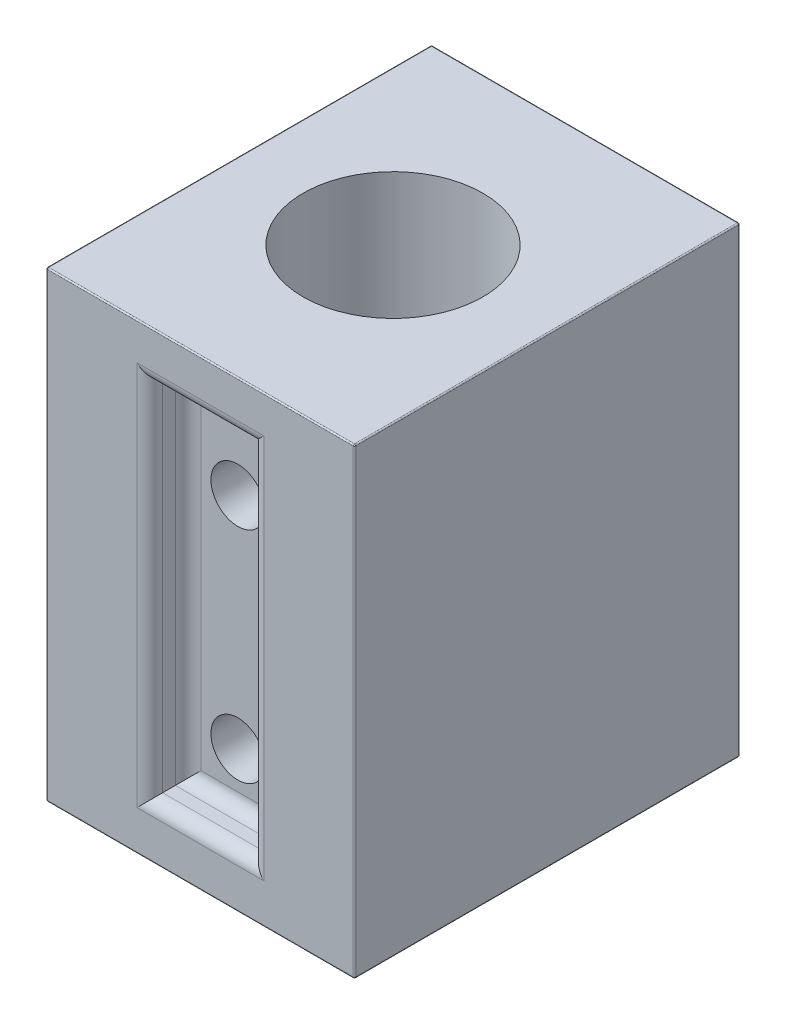
SolidWorks part; units mm, degrees
ref_plane "Front" through (0, 0, 0) normal (0, 0, 1) x (1, 0, 0)
ref_plane "Top" through (0, 0, 0) normal (0, 1, 0) x (1, 0, 0)
ref_plane "Right" through (0, 0, 0) normal (1, 0, 0) x (0, 0, -1)
sketch "Sketch2" plane through (0, 0, 0) normal (0, 0, 1) x (1, 0, 0)
  line L1 (-6, 9) -> (6, 9)
  line L2 (-6, 9) -> (-6, -9)
  line L3 (-6, -9) -> (6, -9)
  line L4 (6, 9) -> (6, -9)
  line L5 (-6, 9) -> (6, -9) construction
  line L6 (-6, -9) -> (6, 9) construction
  point P0 (0, 0)
  dimension "D1" = 12
  dimension "D2" = 18
extrude "Boss-Extrude1" add sketch "Sketch2" along normal blind 15
sketch "Sketch5" plane through (0, -9, 0) normal (0, -1, 0) x (-1, 0, 0)
  line L0 (6, -15) -> (-6, 0) construction
  line L1 (6, -15) -> (-6, -15) construction
  line L2 (-6, -15) -> (6, 0) construction
  line L3 (6, -15) -> (6, 0) construction
  circle A0 centre (0, -7.5) radius 3.5
  dimension "D1" = 7
extrude "Cut-Extrude2" cut sketch "Sketch5" against normal blind 18
sketch "Sketch8" plane through (0, 0, 15) normal (0, 0, 1) x (1, 0, 0)
  line L1 (-1.9685, 7.05) -> (1.9685, 7.05)
  line L2 (-1.9685, 7.05) -> (-1.9685, -6.95)
  line L3 (-1.9685, -6.95) -> (1.9685, -6.95)
  line L4 (1.9685, 7.05) -> (1.9685, -6.95)
  line L6 (6, 9) -> (-6, 9) construction
  point P6 (0, 9)
  point P7 (0, 7.05)
  dimension "D1" = 14
  dimension "D2" = 3.937
  dimension "D3" = 1.95
extrude "Cut-Extrude3" cut sketch "Sketch8" against normal blind 1.4928
fillet "Fillet3" radius 0.05 12 edges at (6, -9, 7.5) (6, 0, 15) (6, 9, 7.5) (6, 0, 0) (-6, 0, 15) (-6, -9, 7.5) (0, -9, 0) (-6, 0, 0) (0, -9, 15) (-6, 9, 7.5) (0, 9, 0) (0, 9, 15)
sketch "Sketch10" plane through (0, 0, 13.5072) normal (0, 0, 1) x (1, 0, 0)
  line L0 (-5.95, 9) -> (5.95, 9) construction
  line L1 (5.95, -9) -> (-5.95, -9) construction
  line L2 (1.9685, -6.95) -> (1.9685, 7.05) construction
  line L3 (1.9685, -6.95) -> (1.9685, 7.05) construction
  circle A0 centre (-0.0315, 3.55) radius 1.05
  circle A1 centre (-0.0315, -5) radius 1.05
  dimension "D2" = 2.1
  dimension "D3" = 2.1
  dimension "D1" = 5.45
  dimension "D4" = 4
  dimension "D5" = 2
  dimension "D6" = 2
extrude "Cut-Extrude6" cut sketch "Sketch10" against normal blind 3 contours A1 | A0
fillet "Fillet9" radius 0.5 4 edges at (0, -6.95, 15) (1.9685, 0.05, 15) (0, 7.05, 15) (-1.9685, 0.05, 15)
fillet "Fillet10" radius 0.5 4 edges at (-1.9685, 0.05, 13.5072) (0, -6.95, 13.5072) (0, 7.05, 13.5072) (1.9685, 0.05, 13.5072)
sketch "Sketch11" plane through (0, -9, 0) normal (0, -1, 0) x (-1, 0, 0)
  line L0 (-5.95, -0.05) -> (5.95, -14.95) construction
  line L1 (5.95, -0.05) -> (-5.95, -14.95) construction
  line L2 (0, -0.05) -> (0, -14.95) construction
  line L3 (5.95, -0.05) -> (-5.95, -0.05) construction
  line L4 (-5.95, -14.95) -> (5.95, -14.95) construction
sketch "Sketch12" plane through (0, 9, 0) normal (0, 1, 0) x (1, 0, 0)
  line L0 (-5.95, -14.95) -> (5.95, -0.05) construction
  line L1 (-5.95, -0.05) -> (5.95, -14.95) construction
  line L2 (0, -14.95) -> (0, -0.05) construction
  line L3 (-5.95, -14.95) -> (5.95, -14.95) construction
  line L4 (5.95, -0.05) -> (-5.95, -0.05) construction
